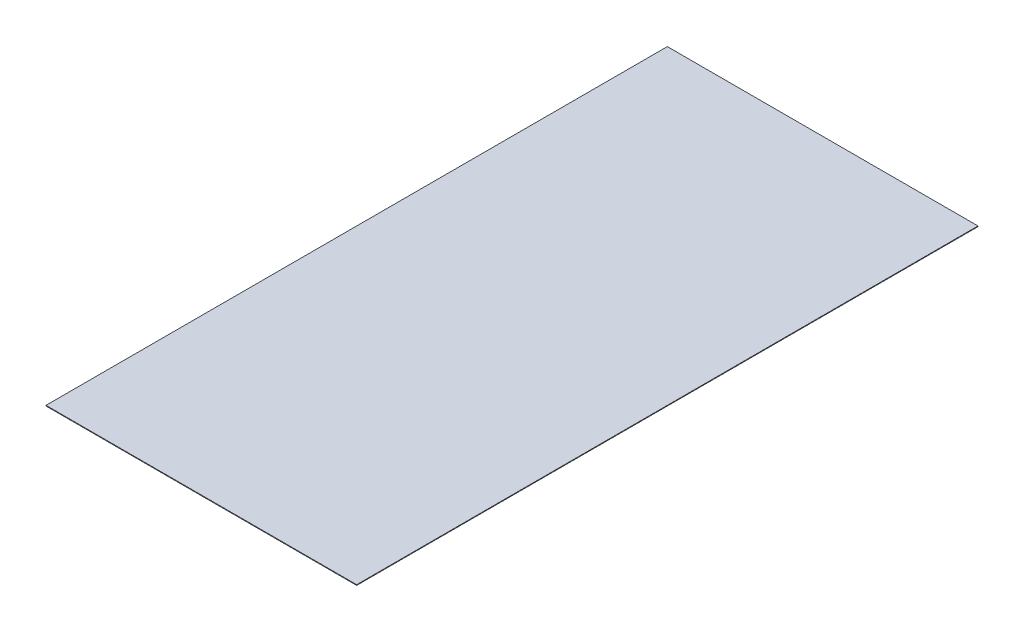
SolidWorks part; units mm, degrees
ref_plane "Front Plane" through (0, 0, 0) normal (0, 0, 1) x (1, 0, 0)
ref_plane "Top Plane" through (0, 0, 0) normal (0, 1, 0) x (1, 0, 0)
ref_plane "Right Plane" through (0, 0, 0) normal (1, 0, 0) x (0, 0, -1)
sketch "Sketch1" plane through (0, 0, 0) normal (0, 1, 0) x (1, 0, 0)
  line L1 (-25, 0) -> (25, 0)
  line L2 (-25, 0) -> (-25, -100)
  line L3 (-25, -100) -> (25, -100)
  line L4 (25, 0) -> (25, -100)
  point P4 (0, 0)
  dimension "D1" = 50
  dimension "D2" = 100
extrude "Boss-Extrude1" add sketch "Sketch1" along normal blind 0.1
